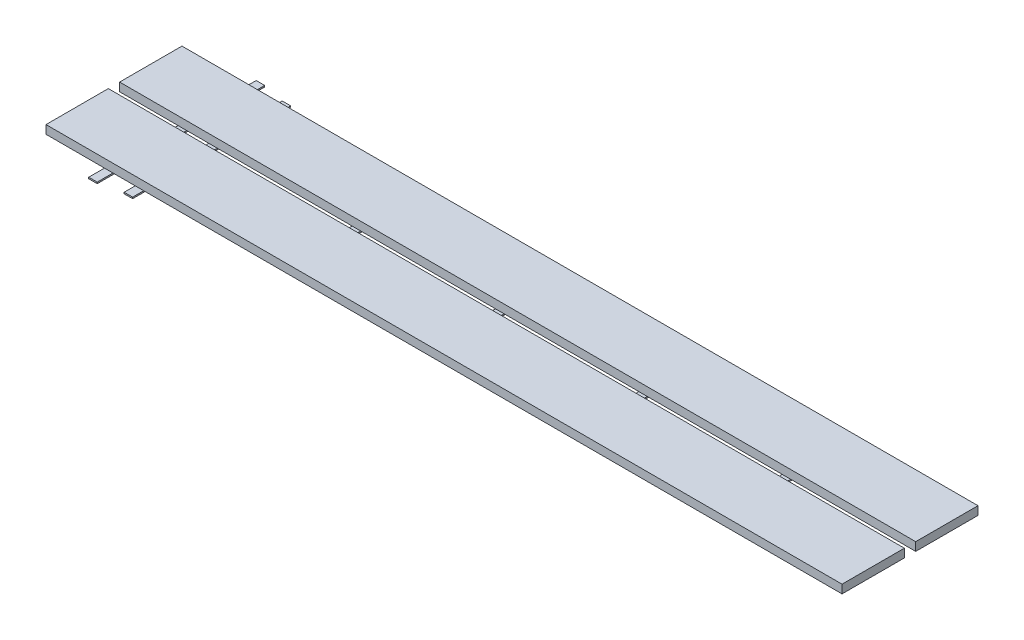
SolidWorks part; units mm, degrees
ref_plane "Front Plane" through (0, 0, 0) normal (0, 0, 1) x (1, 0, 0)
ref_plane "Top Plane" through (0, 0, 0) normal (0, 1, 0) x (1, 0, 0)
ref_plane "Right Plane" through (0, 0, 0) normal (1, 0, 0) x (0, 0, -1)
sketch "Sketch2" plane through (0, 0, 0) normal (0, 1, 0) x (1, 0, 0)
  line L0 (23, 0) -> (23, 355.0006)
  line L1 (23, 355.0006) -> (42.05, 355.0006)
  line L2 (42.05, 355.0006) -> (42.05, 0)
  line L3 (42.05, 0) -> (23, 0)
  line L4 (42.05, 177.5003) -> (23, 177.5003)
  line L5 (32.525, 177.5003) -> (32.525, 167.5003)
  line L6 (32.525, 177.5003) -> (32.525, 187.5003)
  line L7 (55.525, 177.5003) -> (55.525, 167.5003)
  line L8 (55.525, 177.5003) -> (55.525, 187.5003)
  line L9 (78.525, 177.5003) -> (78.525, 167.5003)
  line L10 (78.525, 177.5003) -> (78.525, 187.5003)
  line L11 (101.525, 177.5003) -> (101.525, 167.5003)
  line L12 (101.525, 177.5003) -> (101.525, 187.5003)
  line L13 (124.525, 177.5003) -> (124.525, 167.5003)
  line L14 (124.525, 177.5003) -> (124.525, 187.5003)
  line L15 (147.525, 177.5003) -> (147.525, 167.5003)
  line L16 (147.525, 177.5003) -> (147.525, 187.5003)
  line L17 (170.525, 177.5003) -> (170.525, 167.5003)
  line L18 (170.525, 177.5003) -> (170.525, 187.5003)
  line L19 (193.525, 177.5003) -> (193.525, 167.5003)
  line L20 (193.525, 177.5003) -> (193.525, 187.5003)
  line L21 (216.525, 177.5003) -> (216.525, 167.5003)
  line L22 (216.525, 177.5003) -> (216.525, 187.5003)
  line L23 (239.525, 177.5003) -> (239.525, 167.5003)
  line L24 (239.525, 177.5003) -> (239.525, 187.5003)
  line L25 (262.525, 177.5003) -> (262.525, 167.5003)
  line L26 (262.525, 177.5003) -> (262.525, 187.5003)
  line L27 (285.525, 177.5003) -> (285.525, 167.5003)
  line L28 (285.525, 177.5003) -> (285.525, 187.5003)
  line L29 (308.525, 177.5003) -> (308.525, 167.5003)
  line L30 (308.525, 177.5003) -> (308.525, 187.5003)
  line L31 (331.525, 177.5003) -> (331.525, 167.5003)
  line L32 (331.525, 177.5003) -> (331.525, 187.5003)
  line L33 (354.525, 177.5003) -> (354.525, 167.5003)
  line L34 (354.525, 177.5003) -> (354.525, 187.5003)
  line L35 (377.525, 177.5003) -> (377.525, 167.5003)
  line L36 (377.525, 177.5003) -> (377.525, 187.5003)
  line L37 (400.525, 177.5003) -> (400.525, 167.5003)
  line L38 (400.525, 177.5003) -> (400.525, 187.5003)
  line L39 (423.525, 177.5003) -> (423.525, 167.5003)
  line L40 (423.525, 177.5003) -> (423.525, 187.5003)
  line L41 (446.525, 177.5003) -> (446.525, 167.5003)
  line L42 (446.525, 177.5003) -> (446.525, 187.5003)
  line L43 (469.525, 177.5003) -> (469.525, 167.5003)
  line L44 (469.525, 177.5003) -> (469.525, 187.5003)
  line L45 (492.525, 177.5003) -> (492.525, 167.5003)
  line L46 (492.525, 177.5003) -> (492.525, 187.5003)
  line L47 (515.525, 177.5003) -> (515.525, 167.5003)
  line L48 (515.525, 177.5003) -> (515.525, 187.5003)
  line L49 (538.525, 177.5003) -> (538.525, 167.5003)
  line L50 (538.525, 177.5003) -> (538.525, 187.5003)
  line L51 (561.525, 177.5003) -> (561.525, 167.5003)
  line L52 (561.525, 177.5003) -> (561.525, 187.5003)
  line L53 (584.525, 177.5003) -> (584.525, 167.5003)
  line L54 (584.525, 177.5003) -> (584.525, 187.5003)
  line L55 (607.525, 177.5003) -> (607.525, 167.5003)
  line L56 (607.525, 177.5003) -> (607.525, 187.5003)
  line L57 (630.525, 177.5003) -> (630.525, 167.5003)
  line L58 (630.525, 177.5003) -> (630.525, 187.5003)
  line L59 (653.525, 177.5003) -> (653.525, 167.5003)
  line L60 (653.525, 177.5003) -> (653.525, 187.5003)
  line L61 (676.525, 177.5003) -> (676.525, 167.5003)
  line L62 (676.525, 177.5003) -> (676.525, 187.5003)
  line L63 (699.525, 177.5003) -> (699.525, 167.5003)
  line L64 (699.525, 177.5003) -> (699.525, 187.5003)
  line L65 (722.525, 177.5003) -> (722.525, 167.5003)
  line L66 (722.525, 177.5003) -> (722.525, 187.5003)
  line L67 (745.525, 177.5003) -> (745.525, 167.5003)
  line L68 (745.525, 177.5003) -> (745.525, 187.5003)
  line L69 (768.525, 177.5003) -> (768.525, 167.5003)
  line L70 (768.525, 177.5003) -> (768.525, 187.5003)
  line L71 (791.525, 177.5003) -> (791.525, 167.5003)
  line L72 (791.525, 177.5003) -> (791.525, 187.5003)
  line L73 (814.525, 177.5003) -> (814.525, 167.5003)
  line L74 (814.525, 177.5003) -> (814.525, 187.5003)
  line L75 (837.525, 177.5003) -> (837.525, 167.5003)
  line L76 (837.525, 177.5003) -> (837.525, 187.5003)
  line L77 (860.525, 177.5003) -> (860.525, 167.5003)
  line L78 (860.525, 177.5003) -> (860.525, 187.5003)
  line L79 (883.525, 177.5003) -> (883.525, 167.5003)
  line L80 (883.525, 177.5003) -> (883.525, 187.5003)
  line L81 (906.525, 177.5003) -> (906.525, 167.5003)
  line L82 (906.525, 177.5003) -> (906.525, 187.5003)
  line L83 (929.525, 177.5003) -> (929.525, 167.5003)
  line L84 (929.525, 177.5003) -> (929.525, 187.5003)
  line L85 (952.525, 177.5003) -> (952.525, 167.5003)
  line L86 (952.525, 177.5003) -> (952.525, 187.5003)
  line L87 (975.525, 177.5003) -> (975.525, 167.5003)
  line L88 (975.525, 177.5003) -> (975.525, 187.5003)
  line L89 (998.525, 177.5003) -> (998.525, 167.5003)
  line L90 (998.525, 177.5003) -> (998.525, 187.5003)
  line L91 (1021.525, 177.5003) -> (1021.525, 167.5003)
  line L92 (1021.525, 177.5003) -> (1021.525, 187.5003)
  line L93 (1044.525, 177.5003) -> (1044.525, 167.5003)
  line L94 (1044.525, 177.5003) -> (1044.525, 187.5003)
  line L95 (1067.525, 177.5003) -> (1067.525, 167.5003)
  line L96 (1067.525, 177.5003) -> (1067.525, 187.5003)
  line L97 (1090.525, 177.5003) -> (1090.525, 167.5003)
  line L98 (1090.525, 177.5003) -> (1090.525, 187.5003)
  line L99 (1113.525, 177.5003) -> (1113.525, 167.5003)
  line L100 (1113.525, 177.5003) -> (1113.525, 187.5003)
  line L101 (1136.525, 177.5003) -> (1136.525, 167.5003)
  line L102 (1136.525, 177.5003) -> (1136.525, 187.5003)
  line L103 (-3.95, 177.5003) -> (-23, 177.5003)
  line L104 (-13.475, 177.5003) -> (-13.475, 187.5003)
  line L105 (65.05, 177.5003) -> (46, 177.5003)
  line L106 (88.05, 177.5003) -> (69, 177.5003)
  line L107 (111.05, 177.5003) -> (92, 177.5003)
  line L108 (134.05, 177.5003) -> (115, 177.5003)
  line L109 (157.05, 177.5003) -> (138, 177.5003)
  line L110 (180.05, 177.5003) -> (161, 177.5003)
  line L111 (203.05, 177.5003) -> (184, 177.5003)
  line L112 (226.05, 177.5003) -> (207, 177.5003)
  line L113 (249.05, 177.5003) -> (230, 177.5003)
  line L114 (272.05, 177.5003) -> (253, 177.5003)
  line L115 (295.05, 177.5003) -> (276, 177.5003)
  line L116 (318.05, 177.5003) -> (299, 177.5003)
  line L117 (341.05, 177.5003) -> (322, 177.5003)
  line L118 (364.05, 177.5003) -> (345, 177.5003)
  line L119 (387.05, 177.5003) -> (368, 177.5003)
  line L120 (410.05, 177.5003) -> (391, 177.5003)
  line L121 (433.05, 177.5003) -> (414, 177.5003)
  line L122 (456.05, 177.5003) -> (437, 177.5003)
  line L123 (479.05, 177.5003) -> (460, 177.5003)
  line L124 (502.05, 177.5003) -> (483, 177.5003)
  line L125 (525.05, 177.5003) -> (506, 177.5003)
  line L126 (548.05, 177.5003) -> (529, 177.5003)
  line L127 (571.05, 177.5003) -> (552, 177.5003)
  line L128 (594.05, 177.5003) -> (575, 177.5003)
  line L129 (617.05, 177.5003) -> (598, 177.5003)
  line L130 (640.05, 177.5003) -> (621, 177.5003)
  line L131 (663.05, 177.5003) -> (644, 177.5003)
  line L132 (686.05, 177.5003) -> (667, 177.5003)
  line L133 (709.05, 177.5003) -> (690, 177.5003)
  line L134 (732.05, 177.5003) -> (713, 177.5003)
  line L135 (755.05, 177.5003) -> (736, 177.5003)
  line L136 (778.05, 177.5003) -> (759, 177.5003)
  line L137 (801.05, 177.5003) -> (782, 177.5003)
  line L138 (824.05, 177.5003) -> (805, 177.5003)
  line L139 (847.05, 177.5003) -> (828, 177.5003)
  line L140 (870.05, 177.5003) -> (851, 177.5003)
  line L141 (893.05, 177.5003) -> (874, 177.5003)
  line L142 (916.05, 177.5003) -> (897, 177.5003)
  line L143 (939.05, 177.5003) -> (920, 177.5003)
  line L144 (962.05, 177.5003) -> (943, 177.5003)
  line L145 (985.05, 177.5003) -> (966, 177.5003)
  line L146 (1008.05, 177.5003) -> (989, 177.5003)
  line L147 (1031.05, 177.5003) -> (1012, 177.5003)
  line L148 (1054.05, 177.5003) -> (1035, 177.5003)
  line L149 (1077.05, 177.5003) -> (1058, 177.5003)
  line L150 (1100.05, 177.5003) -> (1081, 177.5003)
  line L151 (1123.05, 177.5003) -> (1104, 177.5003)
  line L152 (1146.05, 177.5003) -> (1127, 177.5003)
  line L153 (-13.475, 177.5003) -> (-13.475, 167.5003)
  line L154 (345, 177.5003) -> (345, 303.0106)
  line L155 (345, 303.0106) -> (364.05, 303.0106)
  line L156 (364.05, 303.0106) -> (364.05, 51.99)
  line L157 (364.05, 51.99) -> (345, 51.99)
  line L158 (345, 51.99) -> (345, 177.5003)
  line L159 (667, 177.5003) -> (667, 266.2276)
  line L160 (667, 266.2276) -> (686.05, 266.2276)
  line L161 (686.05, 266.2276) -> (686.05, 88.773)
  line L162 (686.05, 88.773) -> (667, 88.773)
  line L163 (667, 88.773) -> (667, 177.5003)
  line L164 (989, 177.5003) -> (989, 240.2243)
  line L165 (989, 240.2243) -> (1008.05, 240.2243)
  line L166 (1008.05, 240.2243) -> (1008.05, 114.7763)
  line L167 (1008.05, 114.7763) -> (989, 114.7763)
  line L168 (989, 114.7763) -> (989, 177.5003)
  line L169 (1311, 177.5003) -> (1311, 221.8207)
  line L170 (1311, 221.8207) -> (1330.05, 221.8207)
  line L171 (1330.05, 221.8207) -> (1330.05, 133.1798)
  line L172 (1330.05, 133.1798) -> (1311, 133.1798)
  line L173 (1311, 133.1798) -> (1311, 177.5003)
  line L174 (-26.95, 177.5003) -> (-46, 177.5003)
  line L175 (1159.525, 177.5003) -> (1159.525, 167.5003) [skipped]
  line L176 (1159.525, 177.5003) -> (1159.525, 187.5003) [skipped]
  line L177 (1169.05, 177.5003) -> (1150, 177.5003) [skipped]
  line L178 (-36.475, 177.5003) -> (-36.475, 187.5003)
  line L179 (-36.475, 177.5003) -> (-36.475, 167.5003)
  line L180 (-26.95, 177.5003) -> (-26.95, 365.5543)
  line L181 (-26.95, 365.5543) -> (-46, 365.5543)
  line L182 (-46, 365.5543) -> (-46, -10.5537)
  line L183 (-46, -10.5537) -> (-26.95, -10.5537)
  line L184 (-26.95, -10.5537) -> (-26.95, 177.5003)
  line L185 (-36.475, 177.5003) -> (-36.475, 74.0706)
  line L186 (32.525, 177.5003) -> (32.525, 79.8751)
  line L187 (308.525, 177.5003) -> (308.525, 108.4802)
  line L188 (584.525, 177.5003) -> (584.525, 128.7085)
  line L189 (860.525, 177.5003) -> (860.525, 143.0084)
  line L190 (1136.525, 177.5003) -> (1136.525, 153.1172)
  line L191 (1169.05, 177.5003) -> (1150, 177.5003)
  line L192 (1159.525, 177.5003) -> (1159.525, 187.5003)
  line L193 (1159.525, 177.5003) -> (1159.525, 167.5003)
  line L194 (1192.05, 177.5003) -> (1173, 177.5003)
  line L195 (1182.525, 177.5003) -> (1182.525, 187.5003)
  line L196 (1182.525, 177.5003) -> (1182.525, 167.5003)
  line L197 (1215.05, 177.5003) -> (1196, 177.5003)
  line L198 (1205.525, 177.5003) -> (1205.525, 187.5003)
  line L199 (1205.525, 177.5003) -> (1205.525, 167.5003)
  line L200 (1238.05, 177.5003) -> (1219, 177.5003)
  line L201 (1228.525, 177.5003) -> (1228.525, 187.5003)
  line L202 (1228.525, 177.5003) -> (1228.525, 167.5003)
  line L203 (1261.05, 177.5003) -> (1242, 177.5003)
  line L204 (1251.525, 177.5003) -> (1251.525, 187.5003)
  line L205 (1251.525, 177.5003) -> (1251.525, 167.5003)
  line L206 (1284.05, 177.5003) -> (1265, 177.5003)
  line L207 (1274.525, 177.5003) -> (1274.525, 187.5003)
  line L208 (1274.525, 177.5003) -> (1274.525, 167.5003)
  line L209 (1307.05, 177.5003) -> (1288, 177.5003)
  line L210 (1297.525, 177.5003) -> (1297.525, 187.5003)
  line L211 (1297.525, 177.5003) -> (1297.525, 167.5003)
  line L212 (1330.05, 177.5003) -> (1311, 177.5003)
  line L213 (1320.525, 177.5003) -> (1320.525, 187.5003)
  line L214 (1320.525, 177.5003) -> (1320.525, 167.5003)
  circle A0 centre (-36.475, 74.0706) radius 2
  circle A1 centre (-36.475, 280.93) radius 2
  circle A2 centre (32.525, 79.8751) radius 2
  circle A3 centre (32.525, 275.1254) radius 2
  circle A4 centre (354.525, 108.4802) radius 2
  circle A5 centre (354.525, 246.5203) radius 2
  circle A6 centre (676.525, 128.7085) radius 2
  circle A7 centre (676.525, 226.292) radius 2
  circle A8 centre (998.525, 143.0084) radius 2
  circle A9 centre (998.525, 211.9922) radius 2
  circle A10 centre (1320.525, 153.1172) radius 2
  circle A11 centre (1320.525, 201.8834) radius 2
  dimension "D5" = 9
  dimension "D1" = 50
  dimension "D3" = 2
  dimension "D2" = 50
  dimension "D4" = 2
extrude "Boss-Extrude1" add sketch "Sketch2" along normal blind 3.175
sketch "Sketch3" plane through (0, 3.175, 0) normal (0, 1, 0) x (1, 0, 0)
  line L0 (1330.05, 177.5003) -> (1330.05, 190.2003)
  line L1 (-46, 177.5003) -> (1330.05, 177.5003)
  line L2 (-46, 365.5543) -> (-46, -10.5537) construction
  line L3 (1330.05, 221.8207) -> (1330.05, 133.1798) construction
  line L4 (1330.05, 190.2003) -> (-46, 190.2003)
  line L7 (1330.05, 164.8003) -> (1330.05, 177.5003)
  line L8 (1330.05, 190.2003) -> (1330.05, 330.2003)
  line L9 (1330.05, 330.2003) -> (-46, 330.2003)
  line L10 (-46, 330.2003) -> (-46, 190.2003)
  line L14 (-36.475, 365.5543) -> (-177.385, 365.5543)
  line L15 (-26.95, 365.5543) -> (-46, 365.5543) construction
  line L16 (-46, 330.2003) -> (-177.385, 330.2003)
  line L17 (-177.385, 330.2003) -> (-177.385, 190.2003)
  line L18 (-177.385, 190.2003) -> (-46, 190.2003)
  line L19 (1330.05, 24.8003) -> (1610.805, 24.8003)
  line L20 (1610.805, 24.8003) -> (1610.805, 164.8003)
  line L21 (1610.805, 164.8003) -> (1330.05, 164.8003)
  line L22 (1320.525, 221.8207) -> (1610.805, 221.8207)
  line L23 (1311, 221.8207) -> (1330.05, 221.8207) construction
  line L24 (1330.05, 330.2003) -> (1610.805, 330.2003)
  line L25 (1610.805, 330.2003) -> (1610.805, 190.2003)
  line L26 (1610.805, 190.2003) -> (1330.05, 190.2003)
  line L30 (1330.05, 164.8003) -> (-46, 164.8003)
  line L31 (-177.385, 164.8003) -> (-46, 164.8003)
  line L32 (-177.385, 24.8003) -> (-177.385, 164.8003)
  line L33 (1330.05, 24.8003) -> (-46, 24.8003)
  line L34 (-46, 24.8003) -> (-177.385, 24.8003)
  point P0 (0, 0)
extrude "Boss-Extrude2" add sketch "Sketch3" along normal blind 19
